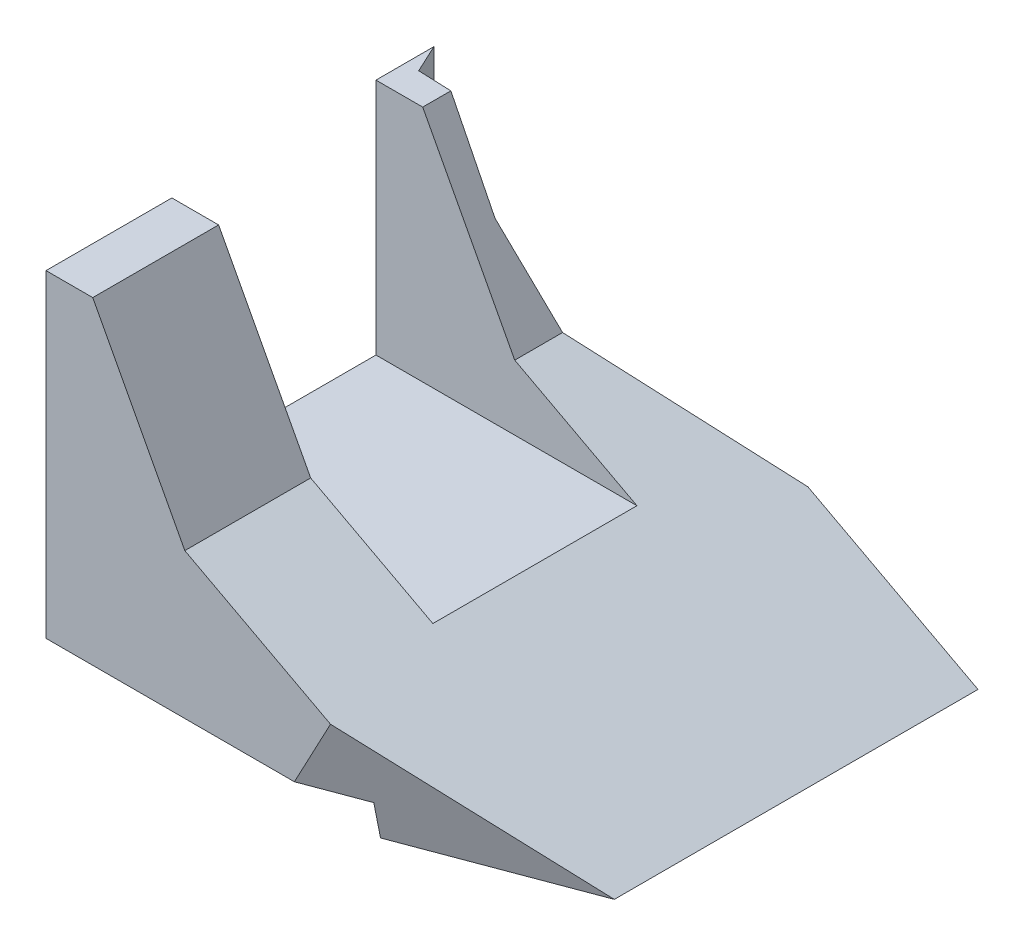
SolidWorks part; units mm, degrees
ref_plane "Alzado" through (0, 0, 0) normal (0, 0, 1) x (1, 0, 0)
ref_plane "Planta" through (0, 0, 0) normal (0, 1, 0) x (1, 0, 0)
ref_plane "Vista lateral" through (0, 0, 0) normal (1, 0, 0) x (0, 0, -1)
sketch "Croquis1" plane through (0, 0, 0) normal (1, 0, 0) x (0, 0, -1)
  line L1 (0, 0) -> (67, 0)
  line L2 (0, 0) -> (0, 51.82)
  line L3 (0, 51.82) -> (67, 51.82)
  line L4 (67, 0) -> (67, 51.82)
  dimension "D1" = 51.82
  dimension "D2" = 67
extrude "Saliente-Extruir1" add sketch "Croquis1" along normal blind 70
sketch "Croquis3" plane through (0, 0, 0) normal (0, 0, 1) x (1, 0, 0)
  line L0 (70, 0) -> (20.4044, 26.3705)
  line L1 (70, 0) -> (0, 0) construction
  line L2 (20.4044, 26.3705) -> (6.8726, 51.82)
  line L3 (70, 51.82) -> (0, 51.82) construction
  line L4 (6.8726, 51.82) -> (70, 51.82)
  line L5 (70, 51.82) -> (70, 0)
  dimension "D1" = 28
  dimension "D2" = 146
extrude "Cortar-Extruir1" cut sketch "Croquis3" against normal up to next
sketch "Croquis4" plane through (0, 51.82, 0) normal (0, 1, 0) x (1, 0, 0)
  line L0 (0, 0) -> (0, 18.5) construction
  line L1 (0, 67) -> (0, 48.5) construction
  line L2 (0, 67) -> (0, 0) construction
  line L4 (0, 18.5) -> (60, 18.5)
  line L5 (0, 18.5) -> (0, 48.5)
  line L6 (0, 48.5) -> (60, 48.5)
  line L7 (60, 18.5) -> (60, 48.5)
  dimension "D1" = 60
extrude "Cortar-Extruir2" cut sketch "Croquis4" against normal blind 35
sketch "Croquis5" plane through (0, 0, 0) normal (0, 0, 1) x (1, 0, 0)
  line L1 (0, 0) -> (45, 0)
  line L2 (0, 0) -> (0, 5)
  line L3 (0, 5) -> (45, 5)
  line L4 (45, 0) -> (45, 5)
  dimension "D1" = 5
  dimension "D2" = 45
extrude "Cortar-Extruir3" cut sketch "Croquis5" against normal up to next
sketch "Croquis6" plane through (0, 51.82, 0) normal (0, 1, 0) x (1, 0, 0)
  line L0 (4.9229, 67) -> (0, 64.3347)
  line L1 (0, 67) -> (4.9229, 67)
  line L2 (6.8726, 67) -> (0, 67) construction
  line L3 (0, 67) -> (0, 64.3347)
  line L4 (0, 67) -> (0, 48.5) construction
extrude "Cortar-Extruir4" cut sketch "Croquis6" against normal up to next
sketch "Croquis9" plane through (0, 51.82, 0) normal (0, 1, 0) x (1, 0, 0)
  line L0 (45, 67) -> (13.6262, 52.3702)
  line L1 (45, 67) -> (-4.6588, 67.0146)
  line L2 (13.6262, 52.3702) -> (1.9544, 52.8324)
  line L3 (1.9544, 52.8324) -> (-4.6588, 67.0146)
extrude "Cortar-Extruir5" cut sketch "Croquis9" against normal up to next
sketch "Croquis11" plane through (0, 0, 0) normal (-1, 0, 0) x (0, 0, 1)
  circle A0 centre (-14.75, 23.32) radius 1.5891
  circle A1 centre (-51.75, 23.32) radius 1.6281
extrude "Cortar-Extruir6" cut sketch "Croquis11" against normal blind 6
sketch "Croquis12" plane through (0, 5, 0) normal (0, -1, 0) x (1, 0, 0)
  line L0 (0, 0) -> (0, -9) construction
  line L1 (0, -57.0237) -> (0, 0) construction
  line L2 (0, -9) -> (10, -9) construction
  line L3 (45, -9) -> (35, -9) construction
  line L4 (45, -67) -> (45, 0) construction
  line L5 (35, -9) -> (35, 0) construction
  line L6 (45, 0) -> (0, 0) construction
  line L7 (10, -9) -> (10, -29) construction
  line L8 (10, -29) -> (35, -29) construction
  line L9 (35, -29) -> (35, -54) construction
  line L10 (10, -52.5138) -> (10, -47.5138) construction
  line L11 (13.6262, -52.3702) -> (1.9544, -52.8324) construction
  circle A0 centre (10, -9) radius 1.75
  circle A1 centre (35, -9) radius 1.75
  circle A2 centre (10, -47.5138) radius 1.75
  circle A3 centre (35, -29) radius 1.75
  circle A4 centre (10, -29) radius 1.75
  circle A5 centre (35, -54) radius 1.75
  dimension "D1" = 3.5
  dimension "D2" = 3.5
  dimension "D3" = 3.5
  dimension "D4" = 3.5
  dimension "D5" = 3.5
  dimension "D6" = 3.5
  dimension "D7" = 10
extrude "Cortar-Extruir7" cut sketch "Croquis12" against normal blind 7
sketch "Croquis14" plane through (15.4282, 29.0163, 0) normal (0.4695, 0.8829, 0) x (0.8829, -0.4695, 0)
  line L0 (25.9788, 18.5) -> (25.9788, -1.66) construction
  line L1 (25.9788, -1.66) -> (66.6988, -1.66)
  line L2 (66.6988, -1.66) -> (66.6988, 15.62)
  line L3 (66.6988, 15.62) -> (25.9788, -1.66)
  dimension "D1" = 40.72
  dimension "D2" = 17.28
extrude "Cortar-Extruir8" cut sketch "Croquis14" against normal up to next
